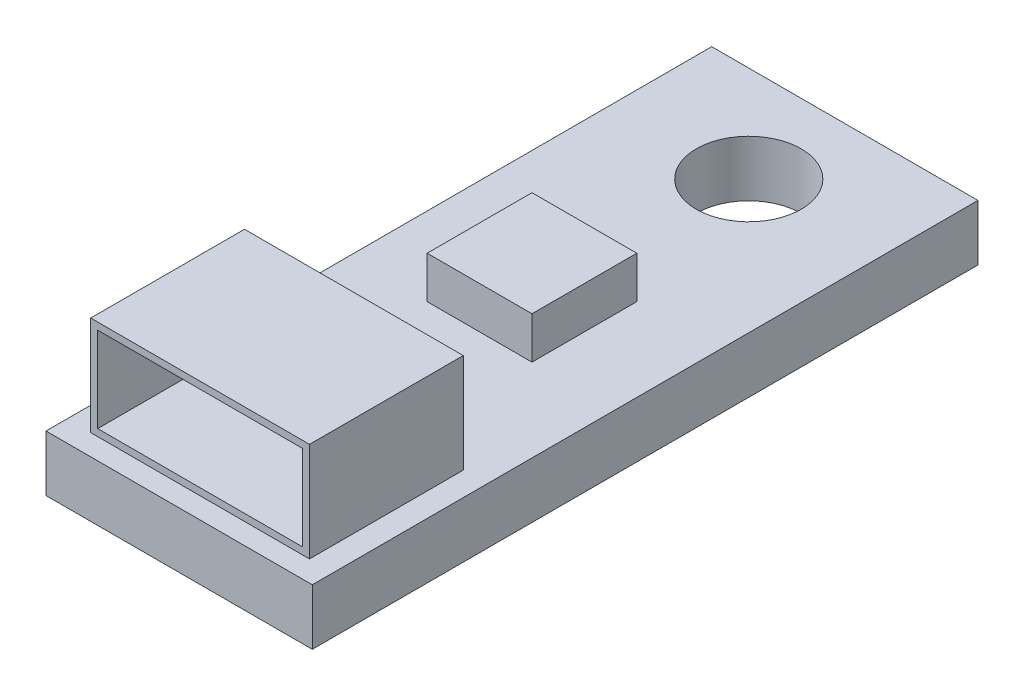
SolidWorks part; units mm, degrees
ref_plane "Front Plane" through (0, 0, 0) normal (0, 0, 1) x (1, 0, 0)
ref_plane "Top Plane" through (0, 0, 0) normal (0, 1, 0) x (1, 0, 0)
ref_plane "Right Plane" through (0, 0, 0) normal (1, 0, 0) x (0, 0, -1)
sketch "Sketch1" plane through (0, 0, 0) normal (0, 1, 0) x (1, 0, 0)
  line L1 (0, 0) -> (7.62, 0)
  line L2 (0, 0) -> (0, 19.05)
  line L3 (0, 19.05) -> (7.62, 19.05)
  line L4 (7.62, 0) -> (7.62, 19.05)
  circle A0 centre (3.81, 16.3) radius 1.5
  point P9 (4.8399, 17.2269)
  dimension "D4" = 3
  dimension "D1" = 7.62
  dimension "D2" = 19.05
  dimension "D3" = 3.81
  dimension "D5" = 2.75
extrude "Boss-Extrude1" add sketch "Sketch1" along normal blind 1.6
sketch "Sketch2" plane through (0, 1.6, 0) normal (0, 1, 0) x (1, 0, 0)
  line L0 (0, 0) -> (7.62, 0) construction
  line L1 (2.2467, 11.66) -> (5.2467, 11.66)
  line L2 (2.2467, 11.66) -> (2.2467, 8.66)
  line L3 (2.2467, 8.66) -> (5.2467, 8.66)
  line L4 (5.2467, 11.66) -> (5.2467, 8.66)
  dimension "D1" = 3
  dimension "D2" = 3
  dimension "D3" = 8.66
extrude "Boss-Extrude2" add sketch "Sketch2" along normal blind 1.2 separate body
sketch "Sketch3" plane through (0, 1.6, 0) normal (0, 1, 0) x (1, 0, 0)
  line L0 (7.62, 0) -> (7.62, 19.05) construction
  line L1 (0.68, 0.6) -> (6.94, 0.6)
  line L2 (0.68, 0.6) -> (0.68, 5)
  line L3 (0.68, 5) -> (6.94, 5)
  line L4 (6.94, 0.6) -> (6.94, 5)
  line L5 (0, 0) -> (7.62, 0) construction
  dimension "D1" = 6.26
  dimension "D2" = 0.68
  dimension "D3" = 0.6
  dimension "D4" = 4.4
extrude "Boss-Extrude3" add sketch "Sketch3" along normal blind 2.84 separate body
sketch "Sketch4" plane through (0, 0, -0.6) normal (0, 0, 1) x (1, 0, 0)
  line L0 (0.88, 1.8) -> (6.74, 1.8)
  line L1 (6.74, 1.8) -> (6.74, 4.24)
  line L2 (6.74, 4.24) -> (0.88, 4.24)
  line L3 (0.88, 4.24) -> (0.88, 1.8)
extrude "Cut-Extrude1" cut sketch "Sketch4" against normal offset from surface (4.2 mm away) 0.2 up to face at (3.81, 3.02, -5)
